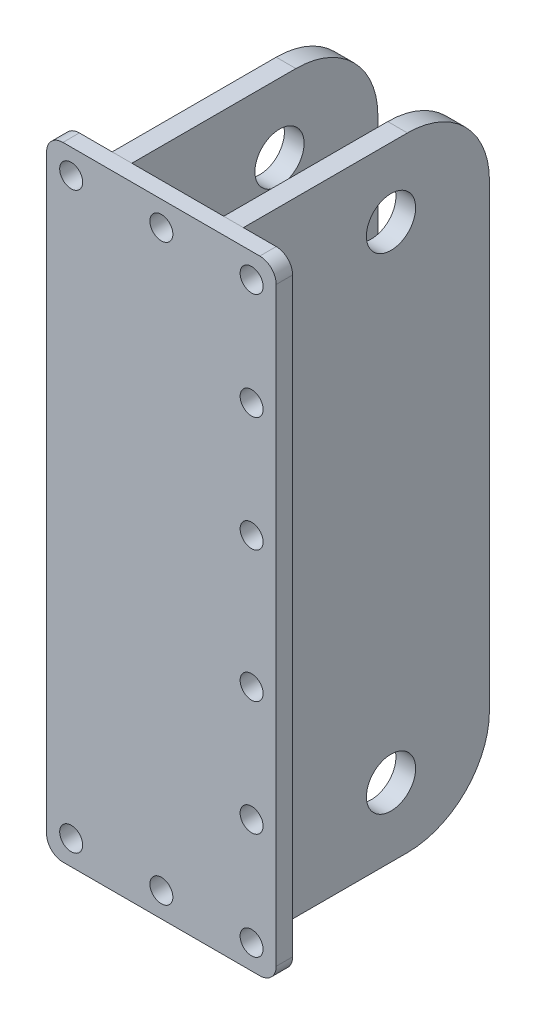
SolidWorks part; units mm, degrees
material "普通碳钢"
ref_plane "前视基准面" through (0, 0, 0) normal (0, 0, 1) x (1, 0, 0)
ref_plane "上视基准面" through (0, 0, 0) normal (0, 1, 0) x (1, 0, 0)
ref_plane "右视基准面" through (0, 0, 0) normal (1, 0, 0) x (0, 0, -1)
sketch "草图1" plane through (0, 0, 0) normal (0, 0, 1) x (1, 0, 0)
  line L1 (10, 0) -> (130, 0)
  line L2 (0, 10) -> (0, 370)
  line L3 (10, 380) -> (130, 380)
  line L4 (140, 10) -> (140, 370)
  arc A0 (130, 0) -> (140, 10) centre (130, 10) ccw
  arc A1 (10, 0) -> (0, 10) centre (10, 10) cw
  arc A2 (130, 380) -> (140, 370) centre (130, 370) cw
  arc A3 (0, 370) -> (10, 380) centre (10, 370) cw
  point P10 (0, 0)
  point P13 (140, 380)
  point P16 (0, 380)
  dimension "D3" = 10
  dimension "D1" = 380
  dimension "D2" = 140
extrude "凸台-拉伸1" add sketch "草图1" along normal blind 10
sketch "草图2" plane through (0, 0, 10) normal (0, 0, 1) x (1, 0, 0)
  line L0 (0, 365) -> (140, 365) construction
  line L1 (0, 370) -> (0, 10) construction
  line L2 (140, 10) -> (140, 370) construction
  line L3 (15, 380) -> (15, 0) construction
  line L4 (130, 380) -> (10, 380) construction
  line L5 (10, 0) -> (130, 0) construction
  line L6 (125, 380) -> (125, 0) construction
  line L7 (0, 15) -> (140, 15) construction
  line L8 (0, 300) -> (140, 300) construction
  line L9 (0, 80) -> (140, 80) construction
  line L10 (0, 230) -> (140, 230) construction
  line L11 (0, 150) -> (140, 150) construction
  circle A0 centre (15, 365) radius 7
  circle A1 centre (125, 365) radius 7
  circle A2 centre (15, 15) radius 7
  circle A3 centre (125, 15) radius 7
  circle A4 centre (70, 365) radius 7
  circle A5 centre (70, 15) radius 7
  circle A8 centre (125, 300) radius 7
  circle A12 centre (125, 80) radius 7
  circle A13 centre (125, 230) radius 7
  circle A14 centre (125, 150) radius 7
  dimension "D1" = 15
  dimension "D5" = 65
  dimension "D9" = 14
  dimension "D2" = 15
  dimension "D3" = 15
  dimension "D4" = 15
  dimension "D6" = 65
  dimension "D7" = 70
  dimension "D8" = 70
extrude "切除-拉伸1" cut sketch "草图2" against normal up to next
sketch "草图3" plane through (0, 0, 0) normal (0, 0, -1) x (-1, 0, 0)
  line L0 (-130, 380) -> (-10, 380) construction
  line L1 (-110, 380) -> (-98, 380)
  line L2 (-110, 380) -> (-110, 0)
  line L3 (-110, 0) -> (-98, 0)
  line L4 (-98, 380) -> (-98, 0)
  line L5 (-10, 0) -> (-130, 0) construction
  line L6 (-42, 380) -> (-30, 380)
  line L7 (-42, 380) -> (-42, 0)
  line L8 (-42, 0) -> (-30, 0)
  line L9 (-30, 380) -> (-30, 0)
  line L10 (-140, 10) -> (-140, 370) construction
  line L11 (0, 370) -> (0, 10) construction
  dimension "D1" = 12
  dimension "D2" = 12
  dimension "D3" = 30
  dimension "D4" = 30
extrude "凸台-拉伸2" add sketch "草图3" along normal blind 150 separate body
fillet "圆角1" radius 50 2 edges at (104, 380, -150) (104, 0, -150)
fillet "圆角2" radius 50 2 edges at (36, 0, -150) (36, 380, -150)
sketch "草图4" plane through (110, 0, 0) normal (1, 0, 0) x (0, 0, -1)
  line L0 (90, 338) -> (90, 42) construction
  line L1 (100, 380) -> (0, 380) construction
  line L3 (100, 0) -> (0, 0) construction
  line L4 (150, 330) -> (150, 50) construction
  circle A0 centre (90, 338) radius 15
  circle A1 centre (90, 42) radius 15
  dimension "D1" = 42
  dimension "D3" = 30
  dimension "D4" = 30
  dimension "D2" = 60
  dimension "D5" = 42
extrude "切除-拉伸2" cut sketch "草图4" against normal up to next (12 mm away)
sketch "草图5" plane through (30, 0, 0) normal (-1, 0, 0) x (0, 0, 1)
  line L0 (-90, 338) -> (-90, 42) construction
  line L1 (-100, 380) -> (0, 380) construction
  line L2 (-100, 0) -> (0, 0) construction
  line L4 (-150, 50) -> (-150, 330) construction
  circle A0 centre (-90, 338) radius 15
  circle A1 centre (-90, 42) radius 15
  dimension "D1" = 42
  dimension "D4" = 30
  dimension "D5" = 30
  dimension "D2" = 42
  dimension "D3" = 60
extrude "切除-拉伸3" cut sketch "草图5" against normal up to next (12 mm away)
